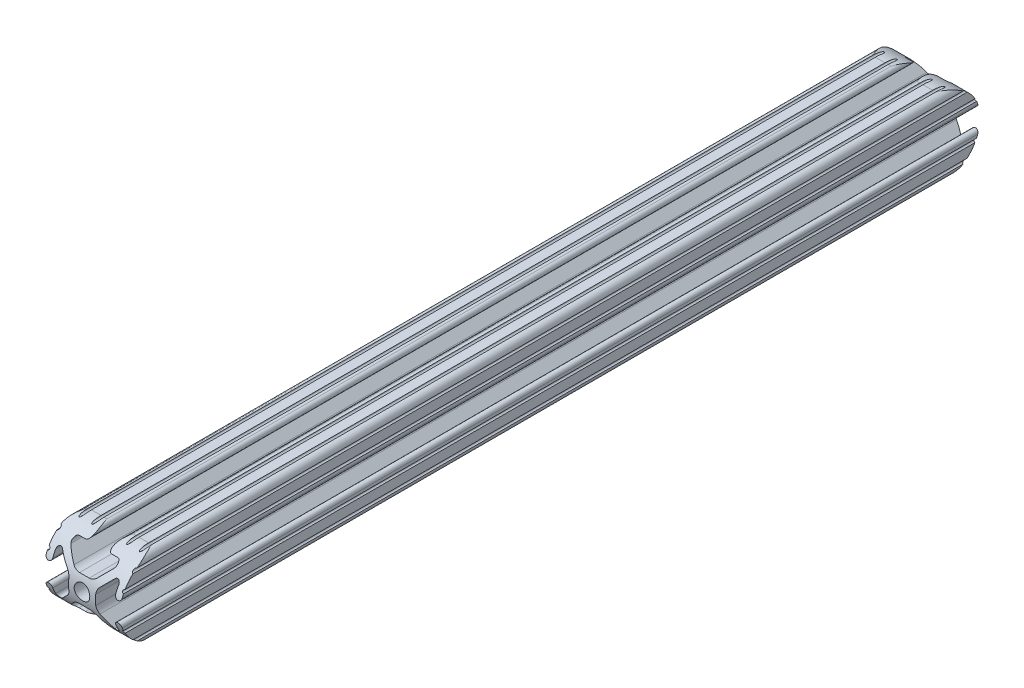
SolidWorks part; units mm, degrees
ref_plane "Front Plane" through (0, 0, 0) normal (0, 0, 1) x (1, 0, 0)
ref_plane "Top Plane" through (0, 0, 0) normal (0, 1, 0) x (1, 0, 0)
ref_plane "Right Plane" through (0, 0, 0) normal (1, 0, 0) x (0, 0, -1)
ref_plane "Plane1" through (0, 0, -450.85) normal (0, 0, -1) x (-1, 0, 0)
sketch "Sketch1" plane through (0, 0, -450.85) normal (0, 0, -1) x (-1, 0, 0)
  line L0 (12.7, -9.5504) -> (12.7, -6.3331)
  line L1 (12.7, -5.3171) -> (12.7, -4.3434)
  line L2 (10.4902, -4.3434) -> (10.4902, -6.4748)
  line L3 (8.7558, -7.1932) -> (5.4257, -3.8632)
  line L4 (4.4958, -1.6181) -> (4.4958, 1.6181)
  line L5 (5.4257, 3.8632) -> (8.7558, 7.1932)
  line L6 (10.4902, 6.4748) -> (10.4902, 4.3434)
  line L7 (12.7, 4.3434) -> (12.7, 5.3171)
  line L8 (12.7, 6.3331) -> (12.7, 9.5504)
  line L9 (9.5504, 12.7) -> (6.3331, 12.7)
  line L10 (5.3171, 12.7) -> (4.3434, 12.7)
  line L11 (4.3434, 10.4902) -> (6.4748, 10.4902)
  line L12 (7.1932, 8.7558) -> (3.8632, 5.4257)
  line L13 (1.6181, 4.4958) -> (-1.6181, 4.4958)
  line L14 (-3.8632, 5.4257) -> (-7.1932, 8.7558)
  line L15 (-6.4748, 10.4902) -> (-4.3434, 10.4902)
  line L16 (-4.3434, 12.7) -> (-5.3171, 12.7)
  line L17 (-6.3331, 12.7) -> (-9.5504, 12.7)
  line L18 (-12.7, 9.5504) -> (-12.7, 6.3331)
  line L19 (-12.7, 5.3171) -> (-12.7, 4.3434)
  line L20 (-10.4902, 4.3434) -> (-10.4902, 6.4748)
  line L21 (-8.7558, 7.1932) -> (-5.4257, 3.8632)
  line L22 (-4.4958, 1.6181) -> (-4.4958, -1.6181)
  line L23 (-5.4257, -3.8632) -> (-8.7558, -7.1932)
  line L24 (-10.4902, -6.4748) -> (-10.4902, -4.3434)
  line L25 (-12.7, -4.3434) -> (-12.7, -5.3171)
  line L26 (-12.7, -6.3331) -> (-12.7, -9.5504)
  line L27 (-9.5504, -12.7) -> (-6.3331, -12.7)
  line L28 (-5.3171, -12.7) -> (-4.3434, -12.7)
  line L29 (-4.3434, -10.4902) -> (-6.4748, -10.4902)
  line L30 (-7.1932, -8.7558) -> (-3.8632, -5.4257)
  line L31 (-1.6181, -4.4958) -> (1.6181, -4.4958)
  line L32 (3.8632, -5.4257) -> (7.1932, -8.7558)
  line L33 (6.4748, -10.4902) -> (4.3434, -10.4902)
  line L34 (4.3434, -12.7) -> (5.3171, -12.7)
  line L35 (6.3331, -12.7) -> (9.5504, -12.7)
  arc A0 (12.6998, -10.5664) -> (12.7, -9.5504) centre (12.7, -10.0584) cw
  arc A1 (12.7, -6.3331) -> (12.7, -5.3171) centre (12.7, -5.8251) cw
  arc A2 (12.7, -4.3434) -> (10.4902, -4.3434) centre (11.5951, -4.3434) ccw
  arc A3 (10.4902, -6.4748) -> (8.7558, -7.1932) centre (9.4742, -6.4748) cw
  arc A4 (5.4257, -3.8632) -> (4.4958, -1.6181) centre (7.6708, -1.6181) cw
  arc A5 (4.4958, 1.6181) -> (5.4257, 3.8632) centre (7.6708, 1.6181) cw
  arc A6 (8.7558, 7.1932) -> (10.4902, 6.4748) centre (9.4742, 6.4748) cw
  arc A7 (10.4902, 4.3434) -> (12.7, 4.3434) centre (11.5951, 4.3434) ccw
  arc A8 (12.7, 5.3171) -> (12.7, 6.3331) centre (12.7, 5.8251) cw
  arc A9 (12.7, 9.5504) -> (12.6998, 10.5664) centre (12.7, 10.0584) cw
  arc A10 (12.6998, 10.5664) -> (10.5664, 12.6998) centre (10.5918, 10.5918) ccw
  arc A11 (10.5664, 12.6998) -> (9.5504, 12.7) centre (10.0584, 12.7) cw
  arc A12 (6.3331, 12.7) -> (5.3171, 12.7) centre (5.8251, 12.7) cw
  arc A13 (4.3434, 12.7) -> (4.3434, 10.4902) centre (4.3434, 11.5951) ccw
  arc A14 (6.4748, 10.4902) -> (7.1932, 8.7558) centre (6.4748, 9.4742) cw
  arc A15 (3.8632, 5.4257) -> (1.6181, 4.4958) centre (1.6181, 7.6708) cw
  arc A16 (-1.6181, 4.4958) -> (-3.8632, 5.4257) centre (-1.6181, 7.6708) cw
  arc A17 (-7.1932, 8.7558) -> (-6.4748, 10.4902) centre (-6.4748, 9.4742) cw
  arc A18 (-4.3434, 10.4902) -> (-4.3434, 12.7) centre (-4.3434, 11.5951) ccw
  arc A19 (-5.3171, 12.7) -> (-6.3331, 12.7) centre (-5.8251, 12.7) cw
  arc A20 (-9.5504, 12.7) -> (-10.5664, 12.6998) centre (-10.0584, 12.7) cw
  arc A21 (-10.5664, 12.6998) -> (-12.6998, 10.5664) centre (-10.5918, 10.5918) ccw
  arc A22 (-12.6998, 10.5664) -> (-12.7, 9.5504) centre (-12.7, 10.0584) cw
  arc A23 (-12.7, 6.3331) -> (-12.7, 5.3171) centre (-12.7, 5.8251) cw
  arc A24 (-12.7, 4.3434) -> (-10.4902, 4.3434) centre (-11.5951, 4.3434) ccw
  arc A25 (-10.4902, 6.4748) -> (-8.7558, 7.1932) centre (-9.4742, 6.4748) cw
  arc A26 (-5.4257, 3.8632) -> (-4.4958, 1.6181) centre (-7.6708, 1.6181) cw
  arc A27 (-4.4958, -1.6181) -> (-5.4257, -3.8632) centre (-7.6708, -1.6181) cw
  arc A28 (-8.7558, -7.1932) -> (-10.4902, -6.4748) centre (-9.4742, -6.4748) cw
  arc A29 (-10.4902, -4.3434) -> (-12.7, -4.3434) centre (-11.5951, -4.3434) ccw
  arc A30 (-12.7, -5.3171) -> (-12.7, -6.3331) centre (-12.7, -5.8251) cw
  arc A31 (-12.7, -9.5504) -> (-12.6998, -10.5664) centre (-12.7, -10.0584) cw
  arc A32 (-12.6998, -10.5664) -> (-10.5664, -12.6998) centre (-10.5918, -10.5918) ccw
  arc A33 (-10.5664, -12.6998) -> (-9.5504, -12.7) centre (-10.0584, -12.7) cw
  arc A34 (-6.3331, -12.7) -> (-5.3171, -12.7) centre (-5.8251, -12.7) cw
  arc A35 (-4.3434, -12.7) -> (-4.3434, -10.4902) centre (-4.3434, -11.5951) ccw
  arc A36 (-6.4748, -10.4902) -> (-7.1932, -8.7558) centre (-6.4748, -9.4742) cw
  arc A37 (-3.8632, -5.4257) -> (-1.6181, -4.4958) centre (-1.6181, -7.6708) cw
  arc A38 (1.6181, -4.4958) -> (3.8632, -5.4257) centre (1.6181, -7.6708) cw
  arc A39 (7.1932, -8.7558) -> (6.4748, -10.4902) centre (6.4748, -9.4742) cw
  arc A40 (4.3434, -10.4902) -> (4.3434, -12.7) centre (4.3434, -11.5951) ccw
  arc A41 (5.3171, -12.7) -> (6.3331, -12.7) centre (5.8251, -12.7) cw
  arc A42 (9.5504, -12.7) -> (10.5664, -12.6998) centre (10.0584, -12.7) cw
  arc A43 (10.5664, -12.6998) -> (12.6998, -10.5664) centre (10.5918, -10.5918) ccw
  circle A44 centre (0, 0) radius 2.6035
extrude "Boss-Extrude1" add sketch "Sketch1" against normal blind 287.02
ref_plane "Plane2" through (-12.7, -9.5504, -450.85) normal (0, 0, -1) x (-1, 0, 0)
sketch "Sketch3" plane through (-12.7, 0, 0) normal (-1, 0, 0) x (0, 0, 1)
  line L0 (-450.85, -1.6181) -> (-450.85, 1.6181) construction
  line L1 (-163.83, -12.6998) -> (-450.85, -12.6998) construction
  line L2 (-163.83, 12.6998) -> (-450.85, 12.6998) construction
  line L3 (-438.1502, -12.6998) -> (-438.1502, -16.2662)
  line L4 (-438.1502, -16.2662) -> (-458.5917, -16.2662)
  line L5 (-458.5917, -16.2662) -> (-458.5917, 14.9464)
  line L6 (-458.5917, 14.9464) -> (-438.1502, 14.9464)
  line L7 (-438.1502, 14.9464) -> (-438.1502, 12.6998)
  line L8 (-163.83, 6.3331) -> (-163.83, 9.5504) construction
  line L9 (-163.83, 12.7) -> (-450.85, 12.7) construction
  line L10 (-163.83, -12.7) -> (-450.85, -12.7) construction
  line L11 (-176.53, -12.7) -> (-176.53, -14.9936)
  line L12 (-176.53, -14.9936) -> (-109.6207, -14.9936)
  line L13 (-109.6207, -14.9936) -> (-109.6207, 14.9464)
  line L14 (-109.6207, 14.9464) -> (-176.53, 14.9464)
  line L15 (-176.53, 14.9464) -> (-176.53, 12.7)
  arc A0 (-438.1502, 12.6998) -> (-438.1502, -12.6998) centre (-438.1502, 0) ccw
  arc A1 (-176.53, -12.7) -> (-176.53, 12.7) centre (-176.53, 0) ccw
extrude "Cut-Extrude1" cut sketch "Sketch3" against normal through all
